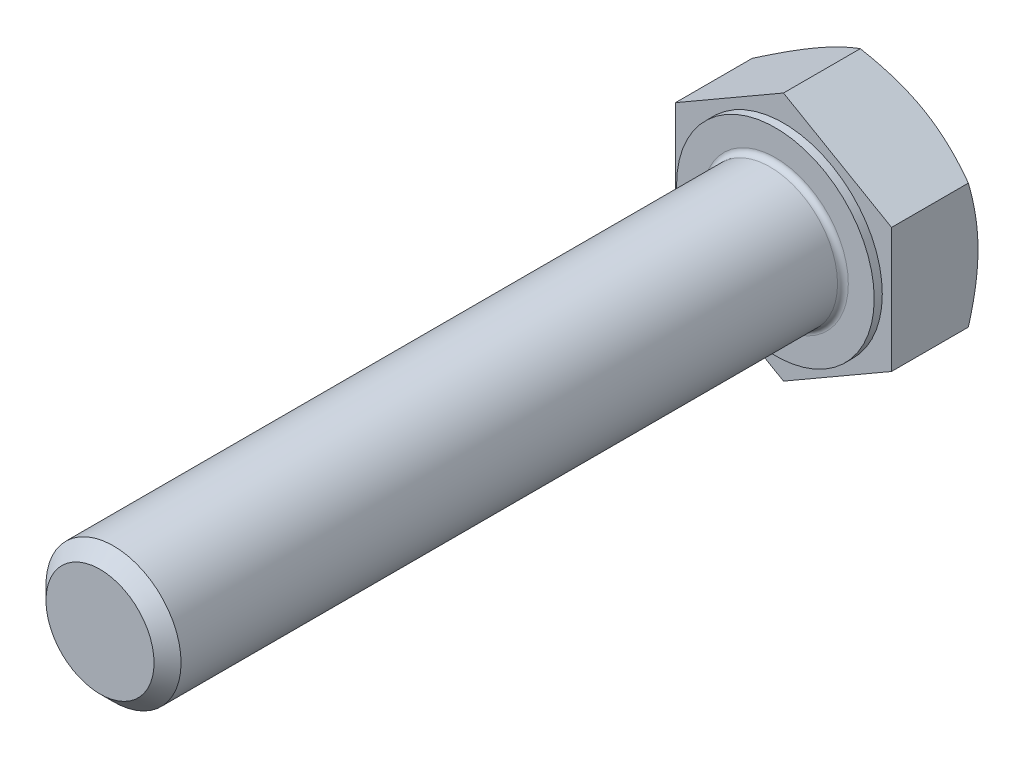
SolidWorks part; units mm, degrees
ref_plane "Přední rovina" through (0, 0, 0) normal (0, 0, 1) x (1, 0, 0)
ref_plane "Vrchní rovina" through (0, 0, 0) normal (0, 1, 0) x (1, 0, 0)
ref_plane "Pravá rovina" through (0, 0, 0) normal (1, 0, 0) x (0, 0, -1)
sketch "Skica1" plane through (0, 0, 0) normal (0, 0, 1) x (1, 0, 0)
  line L1 (8, -4.6188) -> (8, 4.6188)
  line L2 (8, 4.6188) -> (0, 9.2376)
  line L3 (0, 9.2376) -> (-8, 4.6188)
  line L4 (-8, 4.6188) -> (-8, -4.6188)
  line L5 (-8, -4.6188) -> (0, -9.2376)
  line L6 (0, -9.2376) -> (8, -4.6188)
  circle A0 centre (0, 0) radius 8 construction
  dimension "s" = 16
extrude "Vysunout1" add sketch "Skica1" along normal blind 6.4
sketch "Skica2" plane through (0, 0, 0) normal (0, 1, 0) x (1, 0, 0)
  line L0 (8, 0) -> (19.0851, 0)
  line L1 (19.0851, 0) -> (19.0851, -6.4)
  line L2 (19.0851, -6.4) -> (8, 0)
  line L3 (8, -6.4) -> (0, -6.4) construction
  line L4 (0, 0) -> (0, -6.4) construction
  dimension "D1" = 30
revolve "Odebrat otočením1" cut sketch "Skica2" angle 360 about L4
sketch "Skica3" plane through (0, 0, 6.4) normal (0, 0, 1) x (1, 0, 0)
  circle A0 centre (0, 0) radius 7.315
  dimension "dw" = 14.63
extrude "Vysunout2" add sketch "Skica3" along normal blind 0.6
sketch "Skica4" plane through (0, 0, 7) normal (0, 0, 1) x (1, 0, 0)
  circle A0 centre (0, 0) radius 5
  dimension "M" = 10
extrude "Vysunout3" add sketch "Skica4" along normal blind 50
cosmetic thread "Kosmetický závit1" parameters "D2"=8.5
chamfer "Zkosit1" distance 1 angle 45 1 edges at (5, 0, 57)
fillet "Zaoblit1" radius 0.4 1 edges at (5, 0, 7)
equation "\"D1@Zkosit1\" = \"M@Skica4\" * 0.1"
equation "\"D2@Kosmetický závit1\" = 0.85 * \"M@Skica4\""
